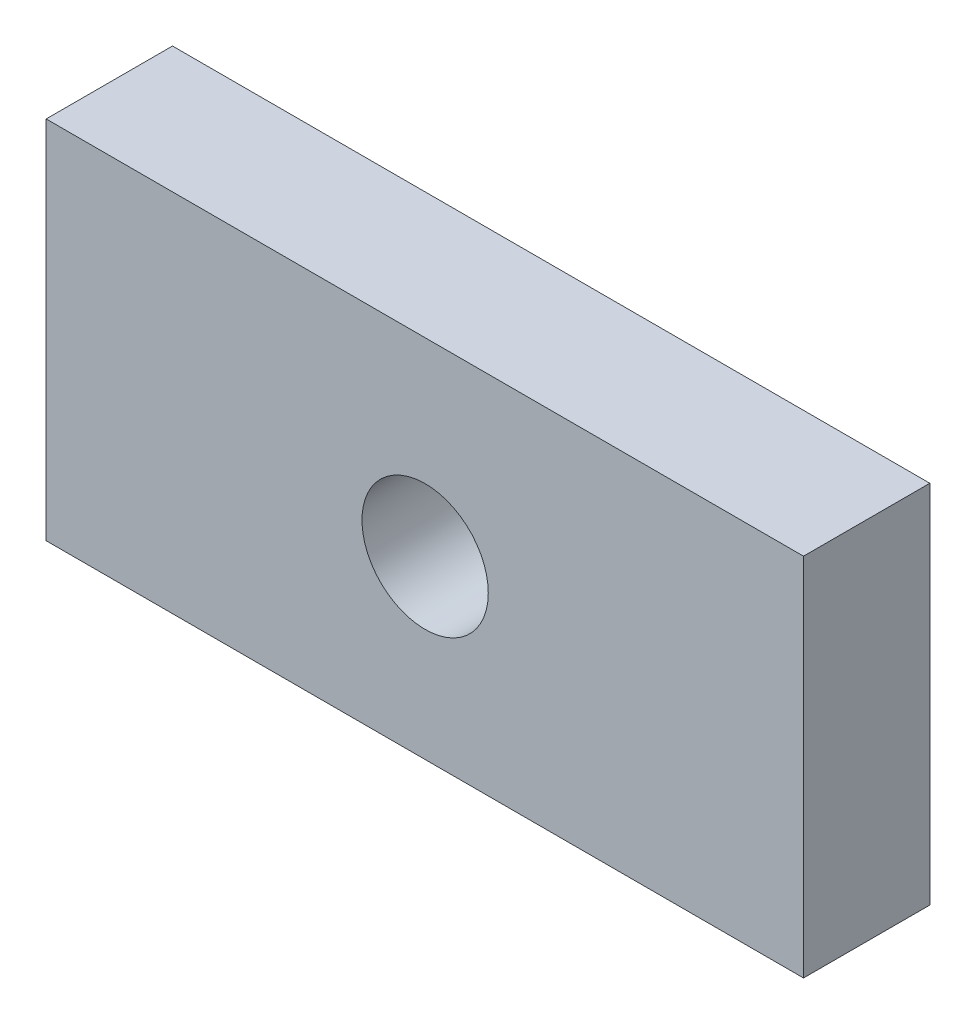
SolidWorks part; units mm, degrees
ref_plane "Front Plane" through (0, 0, 0) normal (0, 0, 1) x (1, 0, 0)
ref_plane "Top Plane" through (0, 0, 0) normal (0, 1, 0) x (1, 0, 0)
ref_plane "Right Plane" through (0, 0, 0) normal (1, 0, 0) x (0, 0, -1)
sketch "Sketch1" plane through (0, 0, 0) normal (0, 0, 1) x (1, 0, 0)
  line L1 (0, 0) -> (76.1426, 0)
  line L2 (0, 0) -> (0, 36.7287)
  line L3 (0, 36.7287) -> (76.1426, 36.7287)
  line L4 (76.1426, 0) -> (76.1426, 36.7287)
extrude "Boss-Extrude1" add sketch "Sketch1" along normal blind 12.7
sketch "Sketch2" plane through (0, 0, 12.7) normal (0, 0, 1) x (1, 0, 0)
  line L0 (0, 36.7287) -> (0, 0) construction
  line L1 (76.1426, 36.7287) -> (0, 36.7287) construction
  circle A0 centre (38.1, 17.6787) radius 6.35
  dimension "D1" = 38.1
  dimension "D2" = 19.05
extrude "Cut-Extrude1" cut sketch "Sketch2" against normal through all
